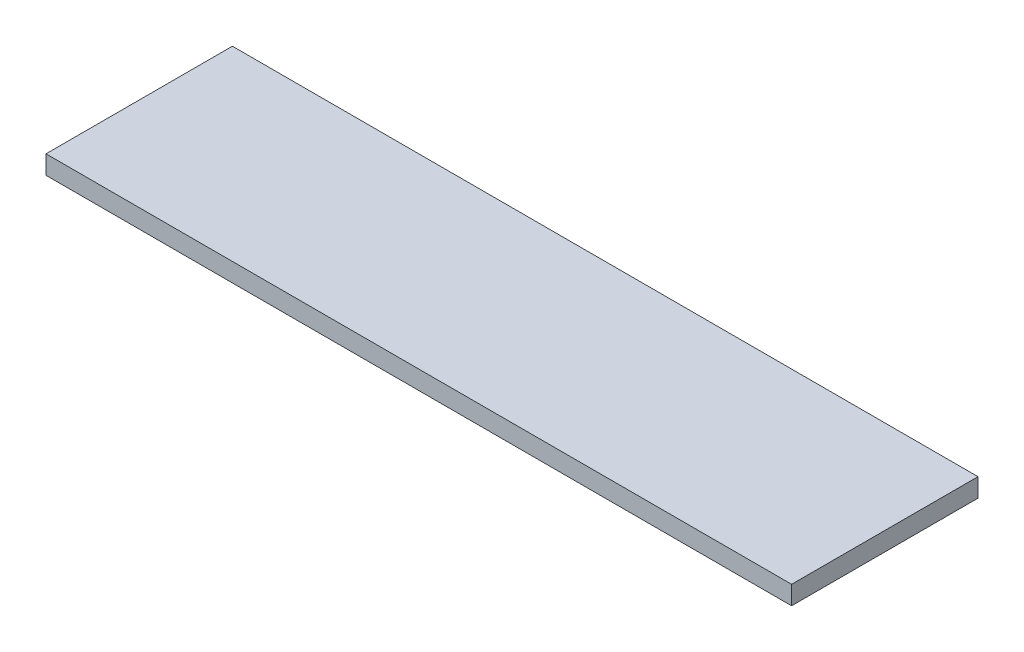
SolidWorks part; units mm, degrees
ref_plane "Front Plane" through (0, 0, 0) normal (0, 0, 1) x (1, 0, 0)
ref_plane "Top Plane" through (0, 0, 0) normal (0, 1, 0) x (1, 0, 0)
ref_plane "Right Plane" through (0, 0, 0) normal (1, 0, 0) x (0, 0, -1)
sketch "Sketch1" plane through (0, 0, 0) normal (0, 1, 0) x (1, 0, 0)
  line L0 (-200, 50) -> (200, -50) construction
  line L1 (-200, 50) -> (200, 50)
  line L2 (-200, 50) -> (-200, -50)
  line L3 (-200, -50) -> (200, -50)
  line L4 (200, 50) -> (200, -50)
  dimension "D1" = 400
  dimension "D2" = 100
extrude "Boss-Extrude1" add sketch "Sketch1" along normal blind 10
